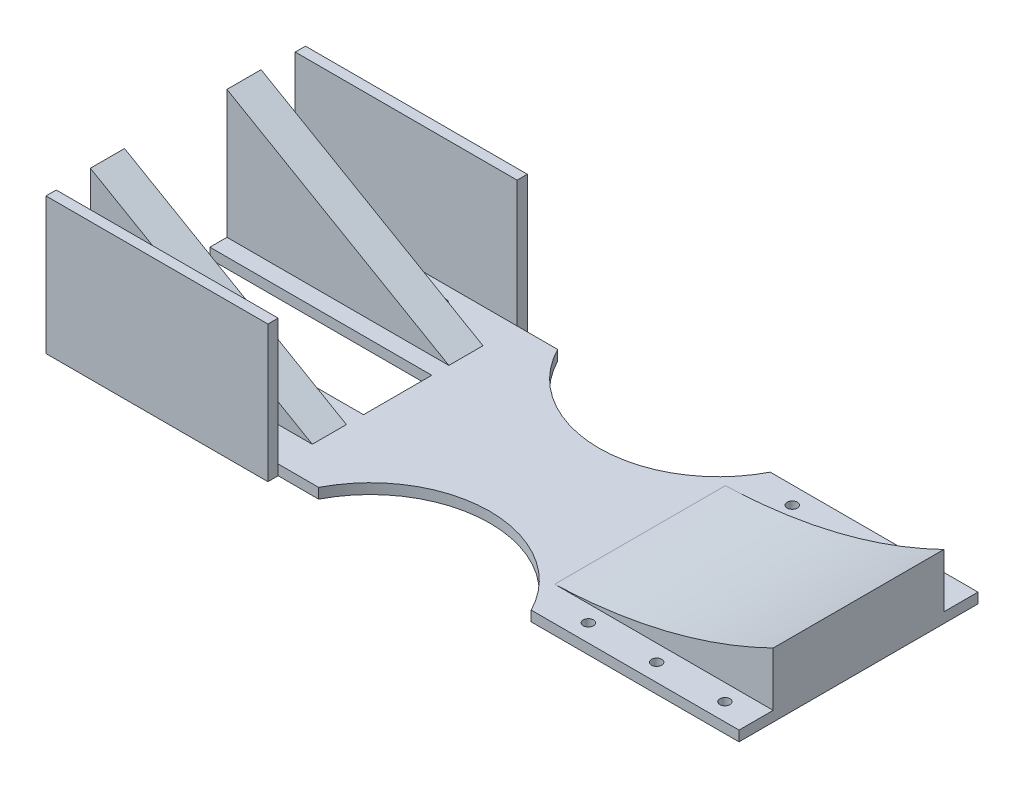
SolidWorks part; units mm, degrees
ref_plane "前视基准面" through (0, 0, 0) normal (0, 0, 1) x (1, 0, 0)
ref_plane "上视基准面" through (0, 0, 0) normal (0, 1, 0) x (1, 0, 0)
ref_plane "右视基准面" through (0, 0, 0) normal (1, 0, 0) x (0, 0, -1)
sketch "草图1" plane through (0, 0, 0) normal (0, 1, 0) x (1, 0, 0)
  line L0 (-92.9537, 0) -> (133.3808, 0) construction
  line L1 (0, 79.573) -> (0, -79.8577) construction
  line L2 (-82.7046, -35) -> (-82.7046, 35)
  line L3 (-82.7046, 35) -> (117.2954, 35)
  line L4 (117.2954, 35) -> (117.2954, -35)
  line L5 (-82.7046, -35) -> (117.2954, -35)
  point P10 (117.2954, 0)
  point P11 (-82.7046, 0)
  dimension "D1" = 70
  dimension "D2" = 200
extrude "凸台-拉伸1" add sketch "草图1" along normal blind 3
sketch "草图2" plane through (0, 0, 0) normal (0, 0, 1) x (1, 0, 0)
  line L0 (-2.7046, 3) -> (-2.7046, 43.2178) construction
  line L1 (-82.7046, 3) -> (117.2954, 3) construction
  line L2 (53.2954, 3) -> (53.2954, 47.8617) construction
  line L3 (-82.7046, 3) -> (-82.7046, 0) construction
  line L5 (-82.7046, 40.5278) -> (-82.7046, 3)
  line L7 (117.2954, 3) -> (117.2954, 18.8104)
  line L8 (53.2954, 3) -> (117.2954, 3)
  line L10 (-82.7046, 3) -> (-17.7046, 3)
  line L11 (-82.7046, 40.5278) -> (-17.7046, 3)
  spline S0 degree 2 poles (53.2954, 3) (87.1934, 4.1023) (117.2954, 18.8104) knots 0 0 0 1 1 1
  dimension "D1" = 56
  dimension "D2" = 80
  dimension "D3" = 30
  dimension "D4" = 65
extrude "凸台-拉伸2" add sketch "草图2" along normal blind 25 and the other way blind 25
sketch "草图6" plane through (-82.7046, 0, 0) normal (-1, 0, 0) x (0, 0, 1)
  line L0 (0, 40.5278) -> (0, 0) construction
  line L1 (-25, 40.5278) -> (25, 40.5278) construction
  line L2 (-15, 40.5278) -> (-15, 3)
  line L3 (-15, 3) -> (15, 3)
  line L4 (15, 3) -> (15, 40.5278)
  line L5 (15, 40.5278) -> (-15, 40.5278)
  dimension "D1" = 15
  dimension "D2" = 15
extrude "切除-拉伸4" cut sketch "草图6" against normal blind 65
ref_plane "基准面1" through (-87.2964, 23.391, 0) normal (-0.9659, 0.2588, 0) x (0, 0, 1)
sketch "草图7" plane through (0, 3, 0) normal (0, 1, 0) x (1, 0, 0)
  line L0 (-2.7046, 35) -> (-2.7046, -35) construction
  line L4 (117.2954, 35) -> (-82.7046, 35) construction
  line L5 (-82.7046, -35) -> (117.2954, -35) construction
  line L6 (-82.7046, 35) -> (-82.7046, 25) construction
  line L7 (53.2954, 35) -> (53.2954, -35) construction
  line L8 (25.2954, 88.1076) -> (25.2954, -100.7895) construction
  line L9 (-82.7046, 0) -> (117.2954, 0) construction
  line L11 (-82.7046, 15) -> (-82.7046, -15) construction
  line L12 (117.2954, 25) -> (117.2954, -25) construction
  circle A0 centre (25.2954, 51) radius 35
  circle A1 centre (25.2954, -51) radius 35
  dimension "D4" = 70
  dimension "D1" = 80
  dimension "D2" = 56
  dimension "D3" = 28
  dimension "D5" = 102
extrude "切除-拉伸5" cut sketch "草图7" against normal through all
sketch "草图8" plane through (-82.7046, 0, 0) normal (-1, 0, 0) x (0, 0, 1)
  line L0 (35, 0) -> (35, 40)
  line L1 (35, 40) -> (38, 40)
  line L2 (38, 40) -> (38, 0)
  line L3 (38, 0) -> (35, 0)
  line L4 (0, 36.5043) -> (0, -13.2047) construction
  line L5 (-38, 0) -> (-35, 0)
  line L6 (-38, 40) -> (-38, 0)
  line L7 (-35, 40) -> (-38, 40)
  line L8 (-35, 0) -> (-35, 40)
  dimension "D1" = 3
  dimension "D2" = 40
extrude "凸台-拉伸3" add sketch "草图8" against normal blind 65
sketch "草图9" plane through (0, 3, 0) normal (0, 1, 0) x (1, 0, 0)
  line L0 (-82.7046, 15) -> (-82.7046, -15) construction
  line L1 (-82.7046, 0) -> (117.2954, 0) construction
  line L2 (117.2954, 25) -> (117.2954, -25) construction
  circle A0 centre (-74.7668, 29.8601) radius 1.5
  circle A1 centre (-54.7668, 29.8601) radius 1.5
  circle A2 centre (-34.7668, 29.8601) radius 1.5
  circle A3 centre (-34.7668, -29.8601) radius 1.5
  circle A4 centre (-54.7668, -29.8601) radius 1.5
  circle A5 centre (-74.7668, -29.8601) radius 1.5
  circle A12 centre (68.0316, 29.8601) radius 1.5
  circle A13 centre (88.0316, 29.8601) radius 1.5
  circle A14 centre (108.0316, 29.8601) radius 1.5
  circle A15 centre (108.0316, -29.8601) radius 1.5
  circle A16 centre (88.0316, -29.8601) radius 1.5
  circle A17 centre (68.0316, -29.8601) radius 1.5
  dimension "D1" = 3
  dimension "D5" = 3
  dimension "D2" = 3
  dimension "D6" = 3
extrude "切除-拉伸6" cut sketch "草图9" against normal through all
sketch "草图11" plane through (0, 3, 0) normal (0, 1, 0) x (1, 0, 0)
  line L0 (-82.7046, 0) -> (117.2954, 0) construction
  line L1 (-82.7046, 15) -> (-82.7046, -15) construction
  line L2 (117.2954, 25) -> (117.2954, -25) construction
  line L3 (-82.7046, -10) -> (-82.7046, 10)
  line L4 (-82.7046, 10) -> (-17.7046, 10)
  line L5 (-17.7046, 10) -> (-17.7046, -10)
  line L6 (-82.7046, -10) -> (-17.7046, -10)
  point P10 (-17.7046, 0)
  dimension "D1" = 20
extrude "切除-拉伸7" cut sketch "草图11" against normal through all
